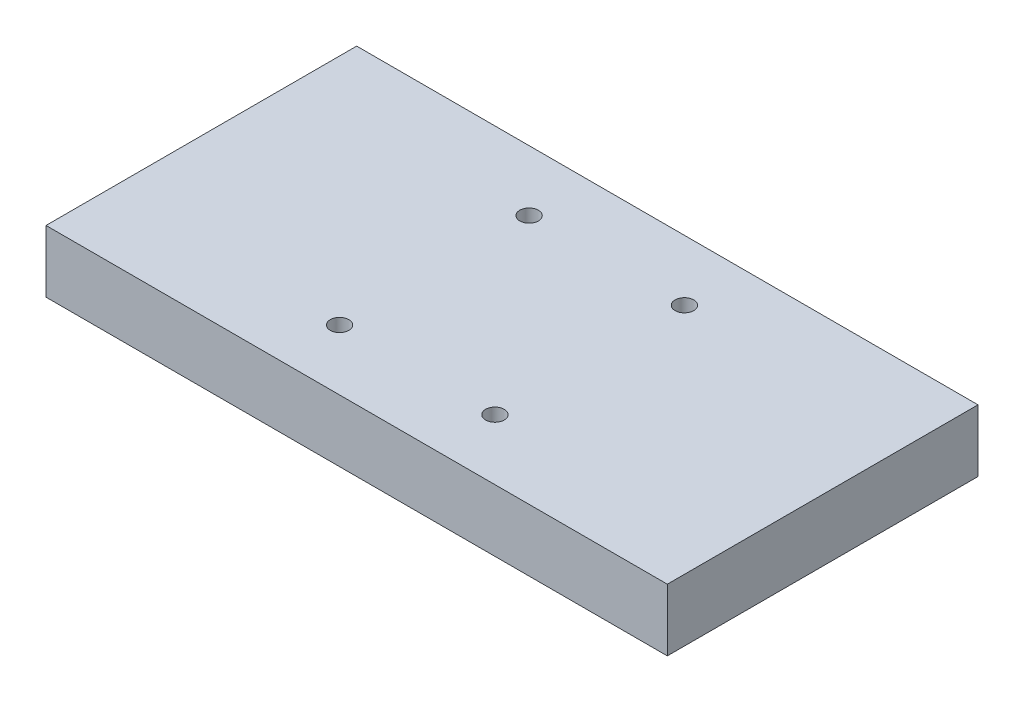
SolidWorks part; units mm, degrees
ref_plane "Front Plane" through (0, 0, 0) normal (0, 0, 1) x (1, 0, 0)
ref_plane "Top Plane" through (0, 0, 0) normal (0, 1, 0) x (1, 0, 0)
ref_plane "Right Plane" through (0, 0, 0) normal (1, 0, 0) x (0, 0, -1)
sketch "Sketch1" plane through (0, 0, 0) normal (0, 1, 0) x (1, 0, 0)
  line L1 (-100, -50) -> (100, -50)
  line L2 (-100, -50) -> (-100, 50)
  line L3 (-100, 50) -> (100, 50)
  line L4 (100, -50) -> (100, 50)
  line L5 (-100, -50) -> (100, 50) construction
  line L6 (-100, 50) -> (100, -50) construction
  point P0 (0, 0)
  dimension "D1" = 100
  dimension "D2" = 200
extrude "Boss-Extrude1" add sketch "Sketch1" along normal blind 20
sketch "Sketch2" plane through (0, 20, 0) normal (0, 1, 0) x (1, 0, 0)
  line L0 (100, 50) -> (-100, 50) construction
  line L1 (-100, 50) -> (-100, -50) construction
  line L2 (-100, -50) -> (100, -50) construction
  line L3 (100, -50) -> (100, 50) construction
  circle A0 centre (-25, 30.5) radius 3
  circle A1 centre (25, -30.5) radius 3
  circle A2 centre (-25, -30.5) radius 3
  circle A3 centre (25, 30.5) radius 3
  dimension "D4" = 6
  dimension "D1" = 61
  dimension "D2" = 50
  dimension "D3" = 61
  dimension "D5" = 19.5
  dimension "D6" = 75
  dimension "D7" = 50
  dimension "D8" = 19.5
  dimension "D9" = 75
extrude "Cut-Extrude1" cut sketch "Sketch2" against normal up to surface (20 mm away) up to face at (0, 0, 0)
sketch "Sketch3" plane through (0, 0, 0) normal (0, -1, 0) x (1, 0, 0)
  line L0 (-100, 50) -> (100, 50) construction
  line L1 (-100, -50) -> (-100, 50) construction
  line L2 (100, -50) -> (-100, -50) construction
  circle A4 centre (25, -30.5) radius 6
  circle A5 centre (-25, -30.5) radius 6
  circle A6 centre (25, 30.5) radius 6
  circle A7 centre (-25, 30.5) radius 6
  circle A8 centre (25, -30.5) radius 3 construction
  point P16 (0, 0)
  point P17 (0, 0)
  dimension "D1" = 12
  dimension "D2" = 19.5
  dimension "D7" = 19.5
  dimension "D3" = 75
  dimension "D4" = 50
  dimension "D5" = 61
  dimension "D6" = 61
  dimension "D8" = 50
  dimension "D9" = 19.5
extrude "Cut-Extrude2" cut sketch "Sketch3" against normal blind 10
